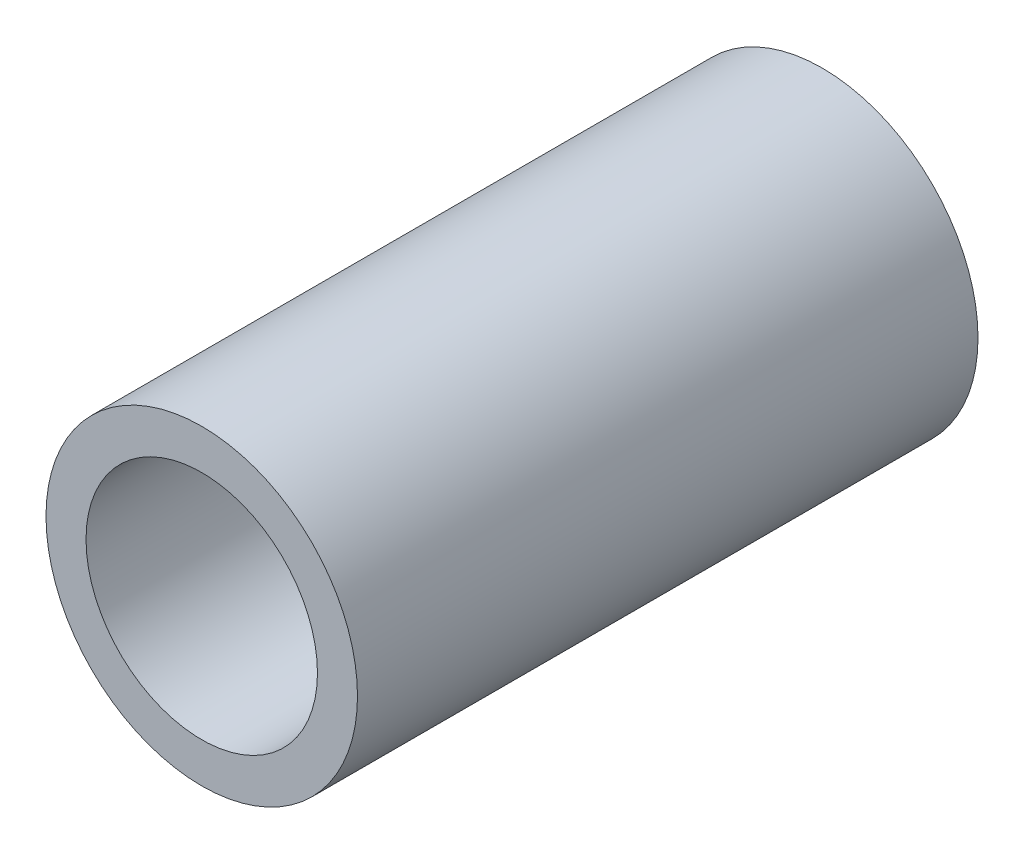
SolidWorks part; units mm, degrees
ref_plane "Front Plane" through (0, 0, 0) normal (0, 0, 1) x (1, 0, 0)
ref_plane "Top Plane" through (0, 0, 0) normal (0, 1, 0) x (1, 0, 0)
ref_plane "Right Plane" through (0, 0, 0) normal (1, 0, 0) x (0, 0, -1)
sketch "Sketch1" plane through (0, 0, 0) normal (0, 0, 1) x (1, 0, 0)
  circle A0 centre (0, 0) radius 3.1877
  circle A1 centre (0, 0) radius 2.3685
  dimension "D1" = 6.3754
  dimension "ID" = 4.7371
extrude "Extrude1" add sketch "Sketch1" along normal mid plane 12.7
sketch "Sketch2" plane through (0, 0, 0) normal (1, 0, 0) x (0, 0, -1)
  line L0 (-6.35, -2.3685) -> (6.35, -2.3685) construction
  line L3 (6.35, 2.3685) -> (-6.35, 2.3685) construction
  line L5 (-6.35, -2.3685) -> (6.35, -2.3685)
  line L6 (6.35, 2.3685) -> (-6.35, 2.3685)
sketch "Sketch4" plane through (0, 0, 6.35) normal (0, 0, 1) x (1, 0, 0)
  line L0 (0, 0) -> (-1.6748, 1.6748)
  line L1 (0, -4.3726) -> (0, 4.3726) construction
  circle A0 centre (0, 0) radius 2.3685 construction
  dimension "D1" = 45
